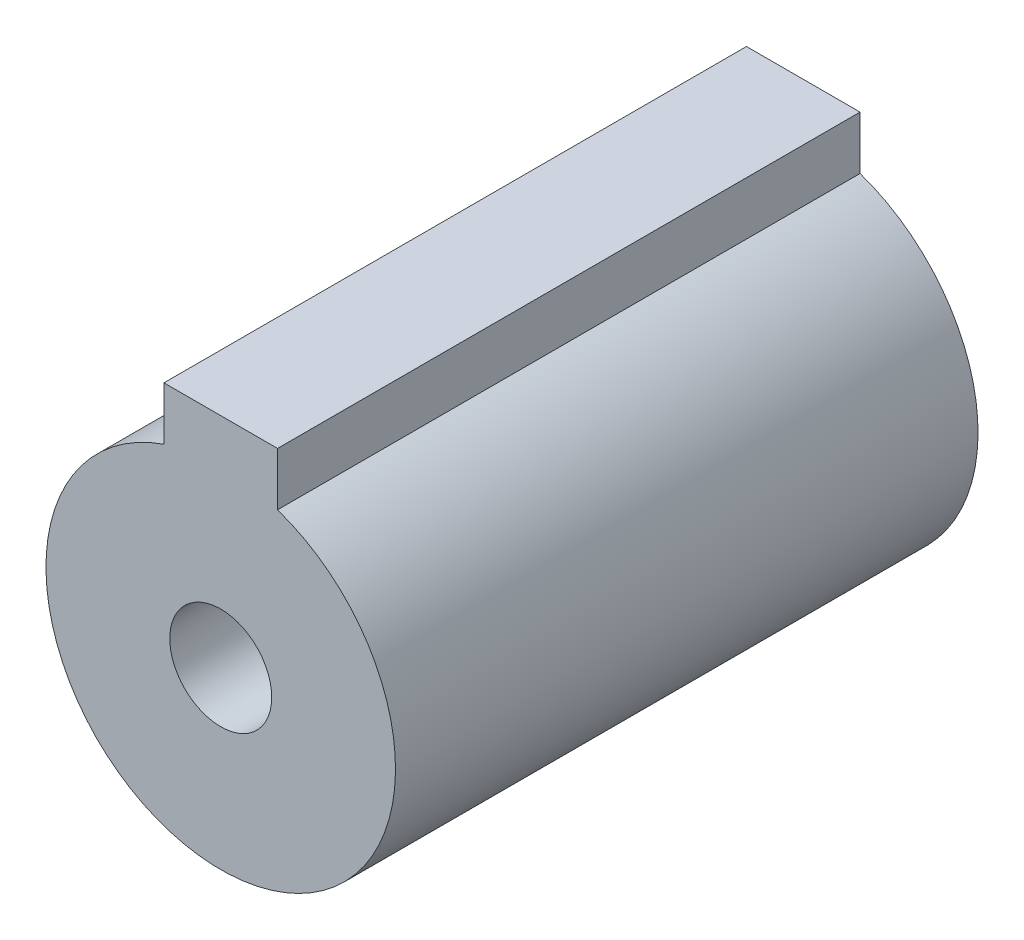
SolidWorks part; units mm, degrees
ref_plane "Plan de face" through (0, 0, 0) normal (0, 0, 1) x (1, 0, 0)
ref_plane "Plan de dessus" through (0, 0, 0) normal (0, 1, 0) x (1, 0, 0)
ref_plane "Plan de droite" through (0, 0, 0) normal (1, 0, 0) x (0, 0, -1)
sketch "Esquisse2" plane through (0, 0, 0) normal (0, 0, 1) x (1, 0, 0)
  circle A0 centre (0, 0) radius 12
extrude "Boss.-Extru.1" add sketch "Esquisse2" along normal blind 40 contours A0
sketch "Esquisse3" plane through (0, 0, 0) normal (0, 0, 1) x (1, 0, 0)
  line L0 (0, -12) -> (-10.6272, -12) construction
  line L1 (4.373, 15) -> (-7.1092, 15) construction
  line L2 (0, 12) -> (-8.1353, 12) construction
  line L3 (0, 12) -> (0, 16.8814) construction
  line L4 (3.9, 17.4677) -> (3.9, 5.3991) construction
  line L5 (-3.9, 19.3732) -> (-3.9, 10.5295) construction
  line L6 (3.9, 15) -> (-3.9, 15)
  line L7 (-3.9, 15) -> (-3.9, 10.9481)
  line L8 (-3.9, 10.9481) -> (3.9, 10.9481)
  line L9 (3.9, 10.9481) -> (3.9, 15)
  circle A1 centre (0, 0) radius 12 construction
  dimension "D1" = 27
  dimension "D2" = 3.9
  dimension "D3" = 3.9
extrude "Boss.-Extru.3" add sketch "Esquisse3" along normal blind 40
sketch "Esquisse4" plane through (0, 0, 0) normal (0, 0, 1) x (1, 0, 0)
  circle A0 centre (0, 0) radius 9.5
extrude "Enlèv. mat.-Extru.3" cut sketch "Esquisse4" along normal blind 32
sketch "Esquisse6" plane through (0, 0, 0) normal (0, 0, 1) x (1, 0, 0)
  line L0 (17.1203, 12.2) -> (-12.2724, 12.2) construction
  line L1 (0, -9.5) -> (-15.2117, -9.5) construction
  line L2 (0, -9.5) -> (0, 16.7499) construction
  line L3 (3, 16.2918) -> (3, -2.9853) construction
  line L4 (-3, 16.2918) -> (-3, 2.4734) construction
  line L5 (3, 12.2) -> (-3, 12.2)
  line L6 (-3, 12.2) -> (-3, 8.3519)
  line L7 (-3, 8.3519) -> (3, 8.3519)
  line L8 (3, 8.3519) -> (3, 12.2)
  circle A0 centre (0, 0) radius 9.5 construction
  circle A1 centre (0, 0) radius 9.5 construction
  dimension "D1" = 21.7
  dimension "D2" = 3
  dimension "D3" = 3
extrude "Enlèv. mat.-Extru.4" cut sketch "Esquisse6" along normal blind 32
sketch "Esquisse7" plane through (0, 0, 0) normal (0, 0, 1) x (1, 0, 0)
  circle A0 centre (0, 0) radius 3.5
extrude "Enlèv. mat.-Extru.5" cut sketch "Esquisse7" along normal blind 42
